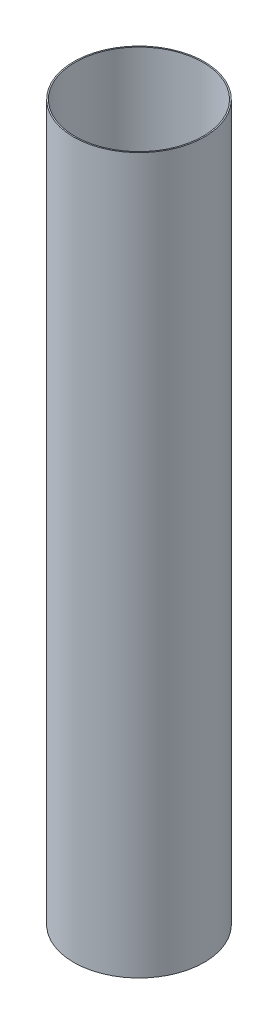
SolidWorks part; units mm, degrees
material "E-Glass Fiber"
ref_plane "Front Plane" through (0, 0, 0) normal (0, 0, 1) x (1, 0, 0)
ref_plane "Top Plane" through (0, 0, 0) normal (0, 1, 0) x (1, 0, 0)
ref_plane "Right Plane" through (0, 0, 0) normal (1, 0, 0) x (0, 0, -1)
sketch "Sketch1" plane through (0, 0, 0) normal (0, 1, 0) x (1, 0, 0)
  circle A0 centre (0, 0) radius 66.04
  circle A1 centre (0, 0) radius 67.31
  dimension "D1" = 132.08
  dimension "D2" = 1.27
extrude "Boss-Extrude1" add sketch "Sketch1" along normal blind 736.6
